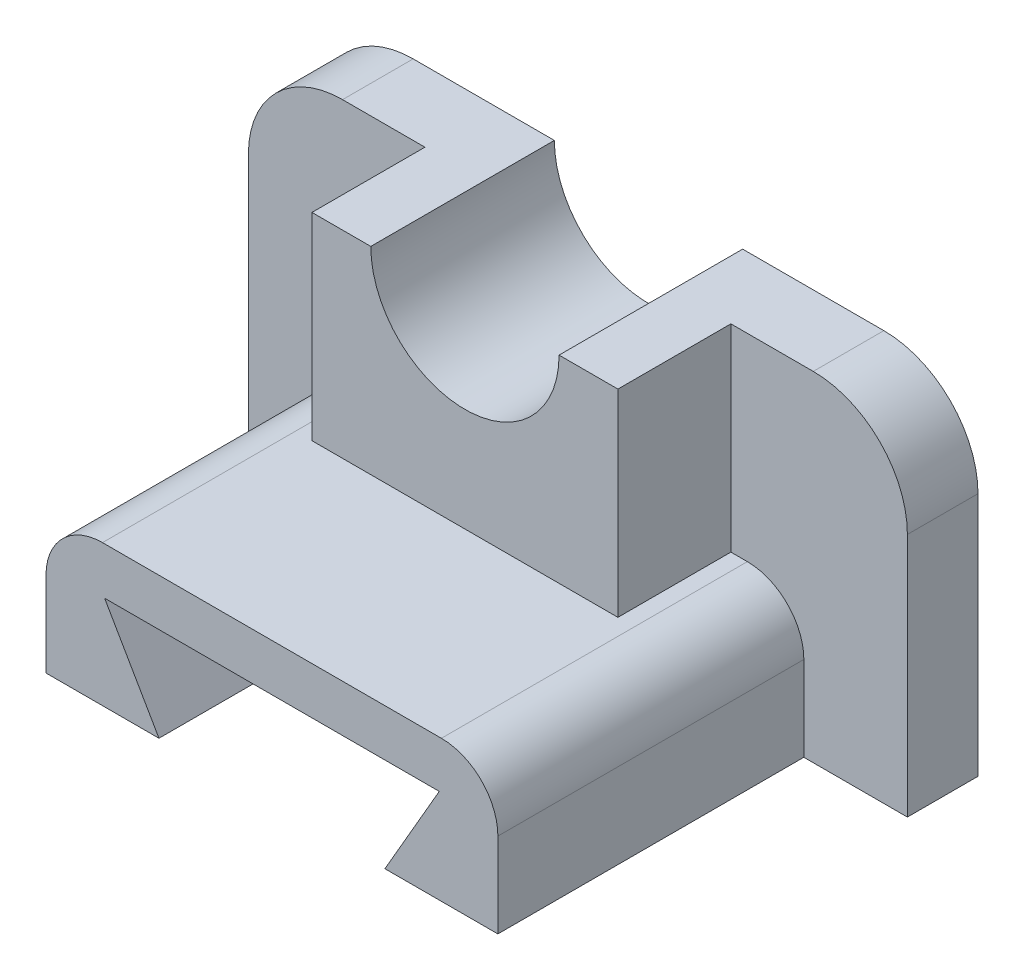
SolidWorks part; units mm, degrees
ref_plane "Ön Düzlem" through (0, 0, 0) normal (0, 0, 1) x (1, 0, 0)
ref_plane "Üst Düzlem" through (0, 0, 0) normal (0, 1, 0) x (1, 0, 0)
ref_plane "Sağ Düzlem" through (0, 0, 0) normal (1, 0, 0) x (0, 0, -1)
sketch "Çizim1" plane through (0, 0, 0) normal (0, 0, 1) x (1, 0, 0)
  line L0 (-100, -72) -> (-120, -72)
  line L1 (0, 0) -> (-100, 0)
  line L3 (0, -72) -> (-100, -72)
  line L5 (-120, -72) -> (-120, -20)
  line L6 (0, -72) -> (20, -72)
  line L7 (20, -72) -> (20, -20)
  line L8 (-82.5, -42) -> (-17.5, -42)
  line L9 (-82.5, 0) -> (-82.5, -42)
  line L10 (-17.5, -42) -> (-17.5, 0)
  arc A0 (-120, -20) -> (-100, 0) centre (-100, -20) cw
  arc A1 (20, -20) -> (0, 0) centre (0, -20) ccw
  point P12 (0, 0)
  dimension "D5" = 20
  dimension "D8" = 20
  dimension "D7" = 20
  dimension "D1" = 100
  dimension "D2" = 72
  dimension "D3" = 20
  dimension "D4" = 52
  dimension "D6" = 52
  dimension "D9" = 17.5
  dimension "D10" = 42
  dimension "D11" = 65
extrude "Yükseklik-Ekstrüzyon1" add sketch "Çizim1" along normal blind 80 contours L7 A1 L1 L10 L8 L9 A0 L5 L0 L3 L6 | L8 L10 L1 L9
sketch "Çizim3" plane through (0, 0, 80) normal (0, 0, 1) x (1, 0, 0)
  line L0 (0, 0) -> (-100, 0) construction
  circle A0 centre (-50, 0) radius 20
  dimension "D1" = 40
extrude "Kes-Ekstrüzyon1" cut sketch "Çizim3" against normal through all contours A0
sketch "Çizim4" plane through (0, 0, 80) normal (0, 0, 1) x (1, 0, 0)
  line L0 (-70, 0) -> (-82.5, 0)
  line L1 (-70, 0) -> (-100, 0) construction
  line L2 (-30, 0) -> (-17.5, 0)
  line L3 (0, 0) -> (-30, 0) construction
  line L4 (-82.5, 0) -> (-100, 0)
  line L5 (-17.5, 0) -> (0, 0)
  line L6 (-82.5, 0) -> (-82.5, -42)
  line L7 (-17.5, 0) -> (-17.5, -42)
  line L8 (-17.5, -42) -> (-82.5, -42)
  arc M3 (-30, 0) -> (-70, 0) centre (-50, 0) cw
  line M4 (-70, 0) -> (-100, 0)
  line M10 (0, 0) -> (-30, 0)
  dimension "D1" = 12.5
  dimension "D2" = 12.5
  dimension "D3" = 42
extrude "Kes-Ekstrüzyon2" cut sketch "Çizim4" against normal blind 41 contours L8 L7 L6 M10 M3 M4
sketch "Çizim5" plane through (0, 0, 80) normal (0, 0, 1) x (1, 0, 0)
  line L0 (-120, -72) -> (-98, -72)
  line L2 (20, -72) -> (-120, -72) construction
  line L3 (20, -72) -> (-2, -72)
  line L4 (-98, -72) -> (-2, -72)
  line L5 (-98, -72) -> (-74, -72)
  line L6 (-2, -72) -> (-26, -72)
  line L7 (-98, -72) -> (-98, -54)
  line L8 (-85.547, -52) -> (-14.453, -52)
  line L9 (-74, -72) -> (-85.547, -52)
  line L10 (-26, -72) -> (-14.453, -52)
  line L11 (-2, -72) -> (-2, -54)
  line L13 (-86, -42) -> (-14, -42)
  arc A0 (-86, -42) -> (-98, -54) centre (-86, -54) ccw
  arc A1 (-2, -54) -> (-14, -42) centre (-14, -54) ccw
  line M3 (-82.5, -42) -> (-82.5, 0)
  line M4 (-82.5, 0) -> (-100, 0)
  arc M5 (-100, 0) -> (-120, -20) centre (-100, -20) ccw
  line M6 (-120, -20) -> (-120, -72)
  line M7 (-120, -72) -> (20, -72)
  line M8 (20, -72) -> (20, -20)
  arc M9 (20, -20) -> (0, 0) centre (0, -20) ccw
  line M10 (0, 0) -> (-17.5, 0)
  line M11 (-17.5, 0) -> (-17.5, -42)
  dimension "D10" = 12
  dimension "D1" = 22
  dimension "D2" = 22
  dimension "D3" = 24
  dimension "D4" = 24
  dimension "D5" = 20
  dimension "D6" = 60
  dimension "D7" = 60
  dimension "D8" = 18
  dimension "D9" = 18
  dimension "D11" = 72
  dimension "D12" = 12
extrude "Kes-Ekstrüzyon5" cut sketch "Çizim5" along direction (0, 0, 1) on the side against the normal blind 65 contours A0 L13 L7 M3 M4 M5 M6 M7 | A1 L11 L13 M7 M8 M9 M10 M11 | L4 L10 L8 L9
sketch "Çizim16" plane through (0, 0, 0) normal (0, 0, 1) x (1, 0, 0)
  line L0 (-74, -72) -> (-85.547, -52)
  line L1 (-85.547, -52) -> (-14.453, -52)
  line L2 (-14.453, -52) -> (-26, -72)
  line L3 (-26, -72) -> (-74, -72)
extrude "Kes-Ekstrüzyon6" cut sketch "Çizim16" against normal through all and the other way blind 156 contours L3 L0 L1 L2
